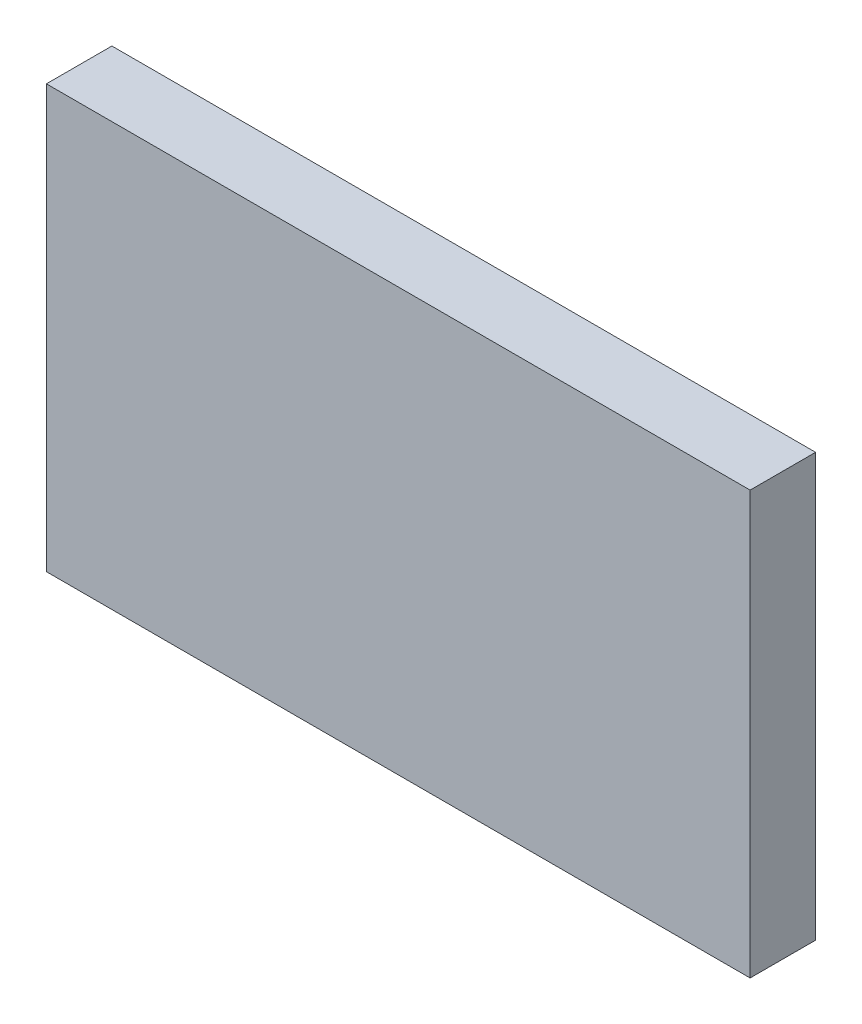
SolidWorks part; units mm, degrees
ref_plane "Plan de face" through (0, 0, 0) normal (0, 0, 1) x (1, 0, 0)
ref_plane "Plan de dessus" through (0, 0, 0) normal (0, 1, 0) x (1, 0, 0)
ref_plane "Plan de droite" through (0, 0, 0) normal (1, 0, 0) x (0, 0, -1)
sketch "Esquisse1" plane through (0, 0, 0) normal (0, 0, 1) x (1, 0, 0)
  line L1 (-59.2864, 30.323) -> (48.1784, 30.323)
  line L2 (-59.2864, 30.323) -> (-59.2864, -34.2044)
  line L3 (-59.2864, -34.2044) -> (48.1784, -34.2044)
  line L4 (48.1784, 30.323) -> (48.1784, -34.2044)
extrude "Boss.-Extru.1" add sketch "Esquisse1" along normal blind 10
